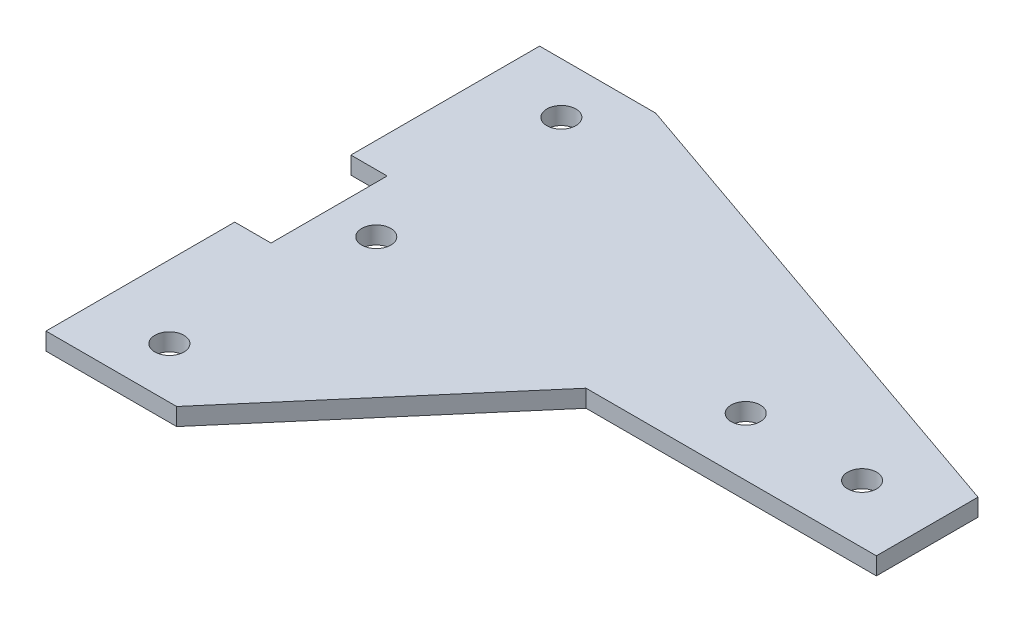
SolidWorks part; units mm, degrees
ref_plane "Front Plane" through (0, 0, 0) normal (0, 0, 1) x (1, 0, 0)
ref_plane "Top Plane" through (0, 0, 0) normal (0, 1, 0) x (1, 0, 0)
ref_plane "Right Plane" through (0, 0, 0) normal (1, 0, 0) x (0, 0, -1)
sketch "Sketch1" plane through (0, 0, 0) normal (0, 1, 0) x (1, 0, 0)
  line L0 (0, 20.32) -> (0, 0)
  line L1 (0, 0) -> (-6.35, 0)
  line L2 (-6.35, 0) -> (-6.35, -33.02)
  line L3 (-6.35, -33.02) -> (16.51, -33.02)
  line L4 (16.51, -33.02) -> (49.551, 5.5667)
  line L5 (49.551, 5.5667) -> (100.351, 5.5667)
  line L6 (100.351, 5.5667) -> (100.351, 23.3467)
  line L8 (-6.35, 53.34) -> (-6.35, 20.32)
  line L9 (-6.35, 20.32) -> (0, 20.32)
  line L10 (-6.35, 53.34) -> (13.97, 53.34)
  line L11 (13.97, 53.34) -> (100.351, 23.3467)
  line L12 (5.715, 10.16) -> (0, 10.16) construction
  circle A0 centre (8.255, 10.16) radius 2.54
  circle A1 centre (87.6892, 15.7267) radius 2.54
  circle A2 centre (6.35, -24.13) radius 2.54
  circle A3 centre (6.35, 44.45) radius 2.54
  circle A4 centre (67.331, 15.7267) radius 2.54
  point P14 (5.715, 10.16)
  point P19 (87.6892, 13.1867)
  point P26 (5.715, -24.13)
  dimension "D10" = 5.08
  dimension "D11" = 5.08
  dimension "D19" = 5.08
  dimension "D20" = 5.08
  dimension "D22" = 5.08
  dimension "D1" = 50.8
  dimension "D2" = 50.8
  dimension "D3" = 22.86
  dimension "D4" = 33.02
  dimension "D5" = 20.32
  dimension "D6" = 20.32
  dimension "D7" = 91.44
  dimension "D8" = 17.78
  dimension "D9" = 6.35
  dimension "D12" = 5.715
  dimension "D13" = 7.62
  dimension "D14" = 79.629
  dimension "D15" = 12.7
  dimension "D16" = 8.89
  dimension "D17" = 8.89
  dimension "D18" = 12.7
  dimension "D21" = 10.16
  dimension "D23" = 33.02
extrude "Boss-Extrude1" add sketch "Sketch1" along normal blind 3.048
